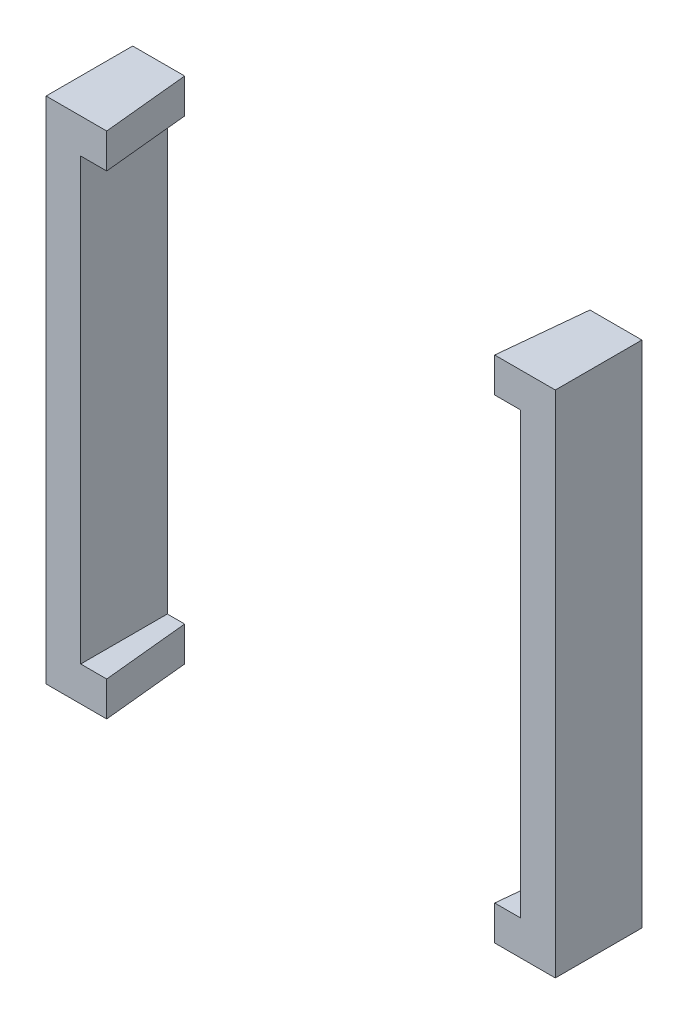
SolidWorks part; units mm, degrees
ref_plane "Front Plane" through (0, 0, 0) normal (0, 0, 1) x (1, 0, 0)
ref_plane "Top Plane" through (0, 0, 0) normal (0, 1, 0) x (1, 0, 0)
ref_plane "Right Plane" through (0, 0, 0) normal (1, 0, 0) x (0, 0, -1)
sketch "草图4" plane through (0, 0, 0) normal (0, 0, 1) x (1, 0, 0)
  line L1 (0, 0) -> (25.4, 0)
  line L2 (0, 0) -> (0, 25.4)
  line L3 (0, 25.4) -> (25.4, 25.4)
  line L4 (25.4, 0) -> (25.4, 25.4)
  dimension "D1" = 25.4
  dimension "D2" = 25.4
extrude "拉伸-薄壁1" add sketch "草图4" along normal blind 5 thin
sketch "草图5" plane through (0, 0, 0) normal (0, 1, 0) x (1, 0, 0)
  line L0 (12.7, 0) -> (12.7, -7.5175) construction
  line L1 (27.4, 0) -> (-2, 0) construction
  line L2 (1, 0) -> (1.5, -5)
  line L3 (27.4, -5) -> (-2, -5) construction
  line L5 (12.7, -5) -> (12.7, 0)
  line L7 (24.4, 0) -> (23.9, -5)
  line L8 (1, 0) -> (24.4, 0)
  line L9 (1.5, -5) -> (23.9, -5)
  point P8 (1.25, -2.5)
  dimension "D1" = 3
  dimension "D2" = 3.5
extrude "切除-拉伸1" cut sketch "草图5" against normal through all and the other way through all contours L8 L7 L9 L2
sketch "草图9" plane through (0, 0, 0) normal (0, 0, 1) x (1, 0, 0)
  line L0 (-2, 27.4) -> (-2, -2) construction
  line L1 (-3.3, 29.7) -> (28.7, 29.7)
  line L2 (-3.3, 29.7) -> (-3.3, -4.3)
  line L3 (-3.3, -4.3) -> (28.7, -4.3)
  line L4 (28.7, 29.7) -> (28.7, -4.3)
  line L5 (27.4, -2) -> (27.4, 27.4) construction
  line L6 (-2, 27.4) -> (-2, -2)
  line L7 (27.4, -2) -> (27.4, 27.4)
  line L8 (-2, 12.7) -> (38.2329, 12.7) construction
  line L9 (-2, 27.4) -> (27.4, 27.4) construction
  line L10 (-2, -2) -> (27.4, -2) construction
  point P10 (-3.3, 12.7)
  point P11 (12.7, -4.3)
  point P12 (12.7, -2)
  dimension "D1" = 32
  dimension "D2" = 34
